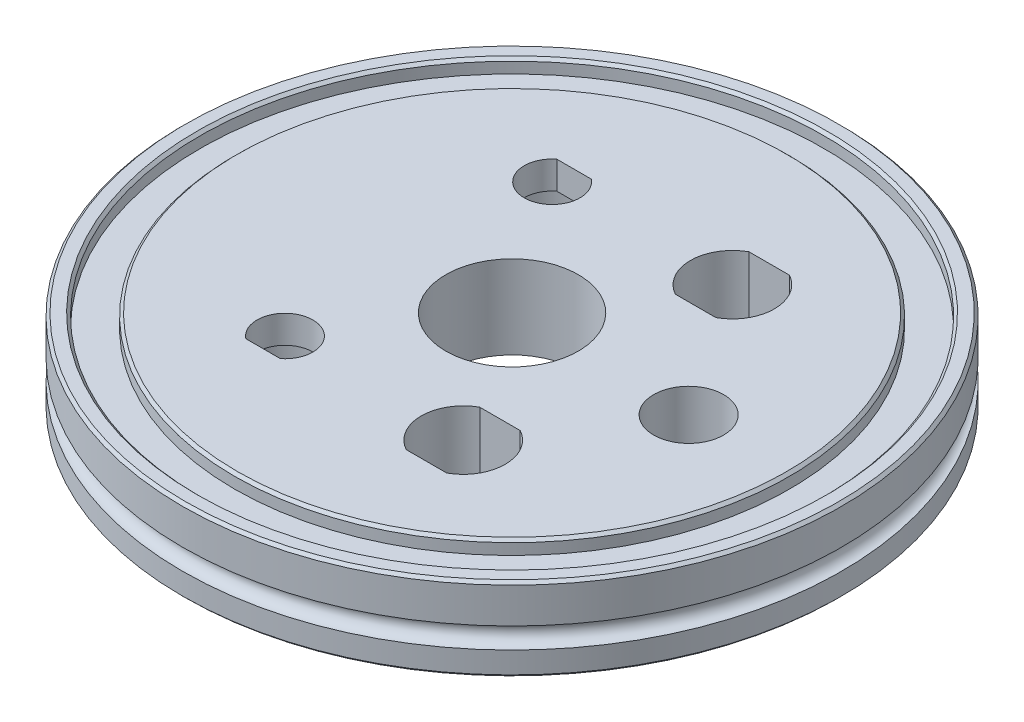
SolidWorks part; units mm, degrees
ref_plane "Front Plane" through (0, 0, 0) normal (0, 0, 1) x (1, 0, 0)
ref_plane "Top Plane" through (0, 0, 0) normal (0, 1, 0) x (1, 0, 0)
ref_plane "Right Plane" through (0, 0, 0) normal (1, 0, 0) x (0, 0, -1)
ref_plane "Plane1" through (0, 0, 0) normal (0, 0, -1) x (-1, 0, 0)
sketch "Sketch1" plane through (0, 0, 0) normal (0, 0, -1) x (-1, 0, 0)
  line L0 (-31.1, 0) -> (0, 0)
  line L1 (0, 0) -> (0, 12)
  line L2 (0, 12) -> (-39.6, 12)
  line L3 (-39.6, 12) -> (-40, 11.6)
  line L4 (-40, 11.6) -> (-40, 10)
  line L5 (-40, 10) -> (-45, 10)
  line L6 (-45, 10) -> (-45, 11.6)
  line L7 (-45, 11.6) -> (-45.4, 12)
  line L8 (-45.4, 12) -> (-47.1, 12)
  line L9 (-47.1, 12) -> (-47.5, 11.6)
  line L10 (-47.5, 11.6) -> (-47.5, 6.5)
  line L11 (-47.5, 3.5) -> (-47.5, 0.4)
  line L12 (-47.5, 0.4) -> (-47.1, 0)
  line L13 (-47.1, 0) -> (-35.4, 0)
  line L14 (-35.4, 0) -> (-35, 0.4)
  line L15 (-35, 0.4) -> (-35, 4.5)
  line L16 (-35, 4.5) -> (-31.5, 4.5)
  line L17 (-31.5, 4.5) -> (-31.5, 0.4)
  line L18 (-31.5, 0.4) -> (-31.1, 0)
  line L19 (0, 0) -> (0, 12) construction
  arc A0 (-47.5, 6.5) -> (-47.5, 3.5) centre (-47.5, 5) cw
revolve "Revolve1" add sketch "Sketch1" angle 360 about L19
sketch "Sketch3" plane through (0, 12, 0) normal (0, 1, 0) x (1, 0, 0)
  line L0 (-10.9932, 22.4093) -> (-15.9649, 22.4093)
  line L1 (0, 0) -> (-25.1, 0) construction
  line L3 (0, 31.084) -> (0, 0) construction
  line L4 (0, 0) -> (19.7116, 30.941) construction
  line L13 (9.4403, 24.698) -> (15.2755, 24.698)
  line L14 (9.4403, 14.098) -> (15.2755, 14.098)
  line L17 (0, 0) -> (-21.5098, 30.7192) construction
  line L18 (-10.9932, -22.4093) -> (-15.9649, -22.4093)
  line L19 (9.4403, -14.098) -> (15.2755, -14.098)
  line L20 (-13.479, 19.2501) -> (-13.479, 30.3915) construction
  line L23 (12.3579, 19.398) -> (12.3579, 32.1804) construction
  line L25 (9.4403, -24.698) -> (15.2755, -24.698)
  circle A0 centre (0, 0) radius 23.5 construction
  arc A1 (-10.9932, 22.4093) -> (-15.9649, 22.4093) centre (-13.479, 19.2501) cw
  circle A3 centre (25.45, 0) radius 5.05
  circle A4 centre (0, 0) radius 23 construction
  arc A9 (9.4403, 24.698) -> (9.4403, 14.098) centre (12.3579, 19.398) ccw
  arc A10 (15.2755, 14.098) -> (15.2755, 24.698) centre (12.3579, 19.398) ccw
  arc A16 (-10.9932, -22.4093) -> (-15.9649, -22.4093) centre (-13.479, -19.2501) ccw
  arc A17 (9.4403, -24.698) -> (9.4403, -14.098) centre (12.3579, -19.398) cw
  arc A18 (15.2755, -14.098) -> (15.2755, -24.698) centre (12.3579, -19.398) cw
  dimension "D1" = 47
  dimension "D5" = 10.1
  dimension "D6" = 4.02
  dimension "D3" = 46
  dimension "D11" = 6.05
  dimension "D13" = 32.5
  dimension "D4" = 25.45
  dimension "D7" = 4.9718
  dimension "D10" = 10.6
  dimension "D14" = 35
extrude "Cut-Extrude1" cut sketch "Sketch3" against normal through all
sketch "Sketch6" plane through (0, 0, 0) normal (0, -1, 0) x (-1, 0, 0)
  line L0 (-37.1199, 0) -> (35.506, 0) construction
  circle A1 centre (13.479, 19.2501) radius 6.95
  circle A2 centre (13.479, -19.2501) radius 6.95
  dimension "D1" = 13.9
extrude "Cut-Extrude2" cut sketch "Sketch6" against normal blind 8
sketch "Sketch7" plane through (0, 12, 0) normal (0, 1, 0) x (1, 0, 0)
  circle A0 centre (0, 0) radius 9.55
  dimension "D1" = 19.1
extrude "Cut-Extrude3" cut sketch "Sketch7" against normal through all contours A0
sketch "Sketch10" plane through (0, 0, 0) normal (0, 0, -1) x (-1, 0, 0)
  line L0 (0, 0) -> (0, 19.3564) construction
sketch "Sketch11" plane through (0, 0, 0) normal (0, -1, 0) x (-1, 0, 0)
  line L0 (-34.2646, 0) -> (34.2646, 0) construction
  circle A1 centre (-12.3579, 19.398) radius 9
  circle A2 centre (-12.3579, -19.398) radius 9
  dimension "D1" = 18
extrude "Cut-Extrude4" [suppressed] cut sketch "Sketch11" against normal blind 8
